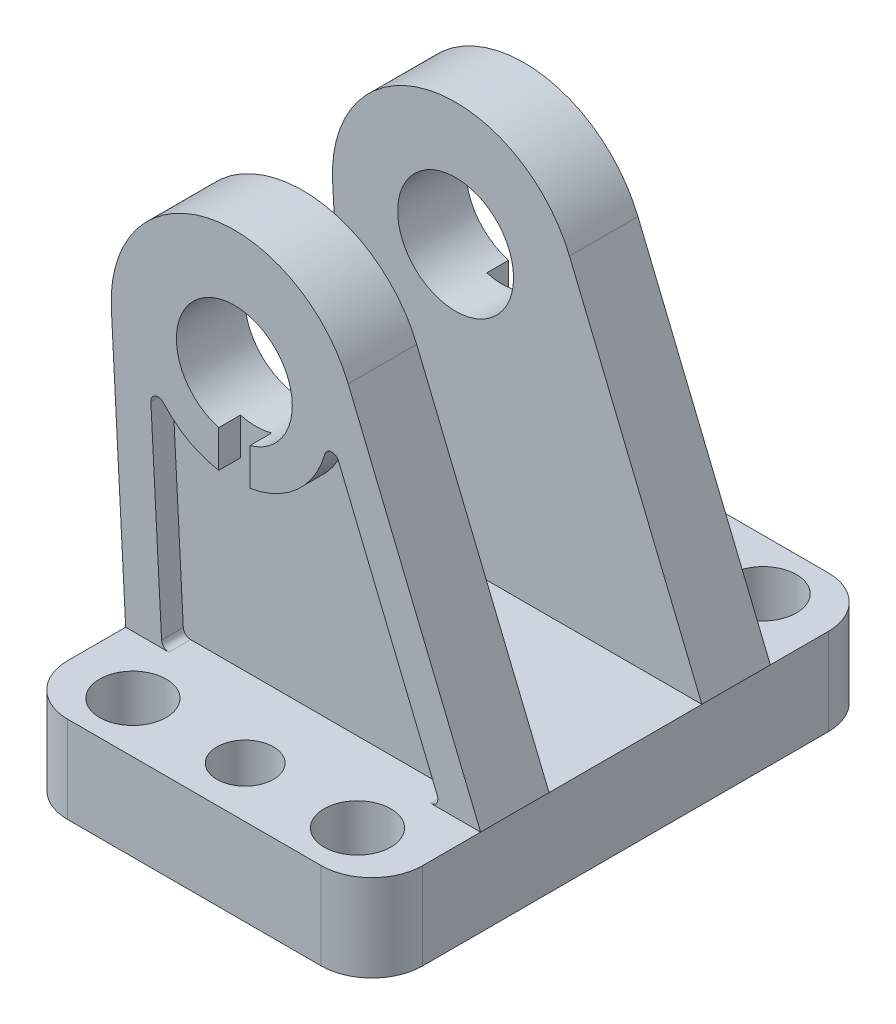
SolidWorks part; units mm, degrees
ref_plane "Front Plane" through (0, 0, 0) normal (0, 0, 1) x (1, 0, 0)
ref_plane "Top Plane" through (0, 0, 0) normal (0, 1, 0) x (1, 0, 0)
ref_plane "Right Plane" through (0, 0, 0) normal (1, 0, 0) x (0, 0, -1)
ref_plane "Plane1" through (0, 0, 0) normal (0, 1, 0) x (1, 0, 0)
sketch "Sketch1" plane through (0, 0, 0) normal (0, 1, 0) x (1, 0, 0)
  line L0 (-17.5, -35) -> (17.5, -35)
  line L1 (24.5, -28) -> (24.5, 28)
  line L2 (17.5, 35) -> (-17.5, 35)
  line L3 (-24.5, 28) -> (-24.5, -28)
  arc A0 (-24.5, -28) -> (-17.5, -35) centre (-17.5, -28) ccw
  arc A1 (17.5, -35) -> (24.5, -28) centre (17.5, -28) ccw
  arc A2 (24.5, 28) -> (17.5, 35) centre (17.5, 28) ccw
  arc A3 (-17.5, 35) -> (-24.5, 28) centre (-17.5, 28) ccw
  circle A4 centre (15.5, 28) radius 4.6
  circle A5 centre (15.5, -28) radius 4.6
  circle A6 centre (0, 28) radius 3.9
  circle A7 centre (0, -28) radius 3.9
  circle A8 centre (-15.5, 28) radius 4.6
  circle A9 centre (-15.5, -28) radius 4.6
extrude "Boss-Extrude1" add sketch "Sketch1" along normal blind 12
ref_plane "Plane2" through (0, 0, 0) normal (0, 1, 0) x (1, 0, 0)
sketch "Sketch2" plane through (0, 0, 0) normal (0, 1, 0) x (1, 0, 0)
  line L0 (-8.9304, -22) -> (8.9304, -22)
  line L1 (19.5, -18.8808) -> (19.5, 18.8808)
  line L2 (8.9304, 22) -> (-8.9304, 22)
  line L3 (-19.5, 18.8808) -> (-19.5, -18.8808)
  arc A0 (-19.5, -18.8808) -> (-18.1875, -19.8307) centre (-18.5, -18.8808) ccw
  arc A1 (-18.1875, -19.8307) -> (-9.6147, -21.7292) centre (-15.5, -28) cw
  arc A2 (-9.6147, -21.7292) -> (-8.9304, -22) centre (-8.9304, -21) ccw
  arc A3 (8.9304, -22) -> (9.6147, -21.7292) centre (8.9304, -21) ccw
  arc A4 (9.6147, -21.7292) -> (18.1875, -19.8307) centre (15.5, -28) cw
  arc A5 (18.1875, -19.8307) -> (19.5, -18.8808) centre (18.5, -18.8808) ccw
  arc A6 (19.5, 18.8808) -> (18.1875, 19.8307) centre (18.5, 18.8808) ccw
  arc A7 (18.1875, 19.8307) -> (9.6147, 21.7292) centre (15.5, 28) cw
  arc A8 (9.6147, 21.7292) -> (8.9304, 22) centre (8.9304, 21) ccw
  arc A9 (-8.9304, 22) -> (-9.6147, 21.7292) centre (-8.9304, 21) ccw
  arc A10 (-9.6147, 21.7292) -> (-18.1875, 19.8307) centre (-15.5, 28) cw
  arc A11 (-18.1875, 19.8307) -> (-19.5, 18.8808) centre (-18.5, 18.8808) ccw
extrude "Cut-Extrude1" cut sketch "Sketch2" along normal blind 6
ref_plane "Plane3" through (0, 0, 20) normal (0, 0, 1) x (1, 0, 0)
sketch "Sketch3" plane through (0, 0, 20) normal (0, 0, 1) x (1, 0, 0)
  line L0 (-26.4759, 49.0958) -> (-24.5, 12)
  line L1 (-24.5, 12) -> (24.5, 12)
  line L2 (24.5, 12) -> (6.2235, 56.4631)
  arc A0 (6.2235, 56.4631) -> (-26.4759, 49.0958) centre (-9.5, 50) ccw
  circle A1 centre (-9.5, 50) radius 8
extrude "Boss-Extrude2" add sketch "Sketch3" against normal blind 9.45
ref_plane "Plane4" through (0, 0, 20) normal (0, 0, 1) x (1, 0, 0)
sketch "Sketch4" plane through (0, 0, 20) normal (0, 0, 1) x (1, 0, 0)
  line L0 (-21.0224, 40.7137) -> (-19.5433, 12.9468)
  line L1 (-18.5448, 12) -> (17.6018, 12)
  line L2 (18.5268, 13.3802) -> (4.8914, 46.5522)
  arc A0 (-19.2721, 41.4264) -> (-21.0224, 40.7137) centre (-20.0238, 40.7669) ccw
  arc A1 (-19.5433, 12.9468) -> (-18.5448, 12) centre (-18.5448, 13) ccw
  arc A2 (17.6018, 12) -> (18.5268, 13.3802) centre (17.6018, 13) ccw
  arc A3 (4.8914, 46.5522) -> (3.0046, 46.4455) centre (3.9665, 46.1721) ccw
  arc A4 (3.0046, 46.4455) -> (-19.2721, 41.4264) centre (-9.5, 50) cw
extrude "Cut-Extrude2" cut sketch "Sketch4" against normal blind 3
ref_plane "Plane5" through (0, 0, -20) normal (0, 0, 1) x (1, 0, 0)
sketch "Sketch5" plane through (0, 0, -20) normal (0, 0, 1) x (1, 0, 0)
  line L0 (-26.4759, 49.0958) -> (-24.5, 12)
  line L1 (-24.5, 12) -> (24.5, 12)
  line L2 (24.5, 12) -> (6.2235, 56.4631)
  arc A0 (6.2235, 56.4631) -> (-26.4759, 49.0958) centre (-9.5, 50) ccw
  circle A1 centre (-9.5, 50) radius 8
extrude "Boss-Extrude3" add sketch "Sketch5" along normal blind 9.45
ref_plane "Plane6" through (0, 0, -20) normal (0, 0, 1) x (1, 0, 0)
sketch "Sketch6" plane through (0, 0, -20) normal (0, 0, 1) x (1, 0, 0)
  line L0 (-21.0224, 40.7137) -> (-19.5433, 12.9468)
  line L1 (-18.5448, 12) -> (17.6018, 12)
  line L2 (18.5268, 13.3802) -> (4.8914, 46.5522)
  arc A0 (-19.2721, 41.4264) -> (-21.0224, 40.7137) centre (-20.0238, 40.7669) ccw
  arc A1 (-19.5433, 12.9468) -> (-18.5448, 12) centre (-18.5448, 13) ccw
  arc A2 (17.6018, 12) -> (18.5268, 13.3802) centre (17.6018, 13) ccw
  arc A3 (4.8914, 46.5522) -> (3.0046, 46.4455) centre (3.9665, 46.1721) ccw
  arc A4 (3.0046, 46.4455) -> (-19.2721, 41.4264) centre (-9.5, 50) cw
extrude "Cut-Extrude3" cut sketch "Sketch6" along normal blind 3
ref_plane "Plane7" through (0, 0, 20) normal (0, 0, 1) x (1, 0, 0)
sketch "Sketch7" plane through (0, 0, 20) normal (0, 0, 1) x (1, 0, 0)
  line L0 (-7.35, 35.15) -> (-7.35, 50)
  line L1 (-7.35, 50) -> (-11.65, 50)
  line L2 (-11.65, 50) -> (-11.65, 35.15)
  arc A0 (-11.65, 35.15) -> (-7.35, 35.15) centre (-9.5, 35.15) ccw
extrude "Cut-Extrude4" cut sketch "Sketch7" against normal blind 3 and the other way blind 3
ref_plane "Plane8" through (0, 0, -20) normal (0, 0, 1) x (1, 0, 0)
sketch "Sketch8" plane through (0, 0, -20) normal (0, 0, 1) x (1, 0, 0)
  line L0 (-7.35, 35.15) -> (-7.35, 50)
  line L1 (-7.35, 50) -> (-11.65, 50)
  line L2 (-11.65, 50) -> (-11.65, 35.15)
  arc A0 (-11.65, 35.15) -> (-7.35, 35.15) centre (-9.5, 35.15) ccw
extrude "Cut-Extrude5" cut sketch "Sketch8" against normal blind 3 and the other way blind 3
